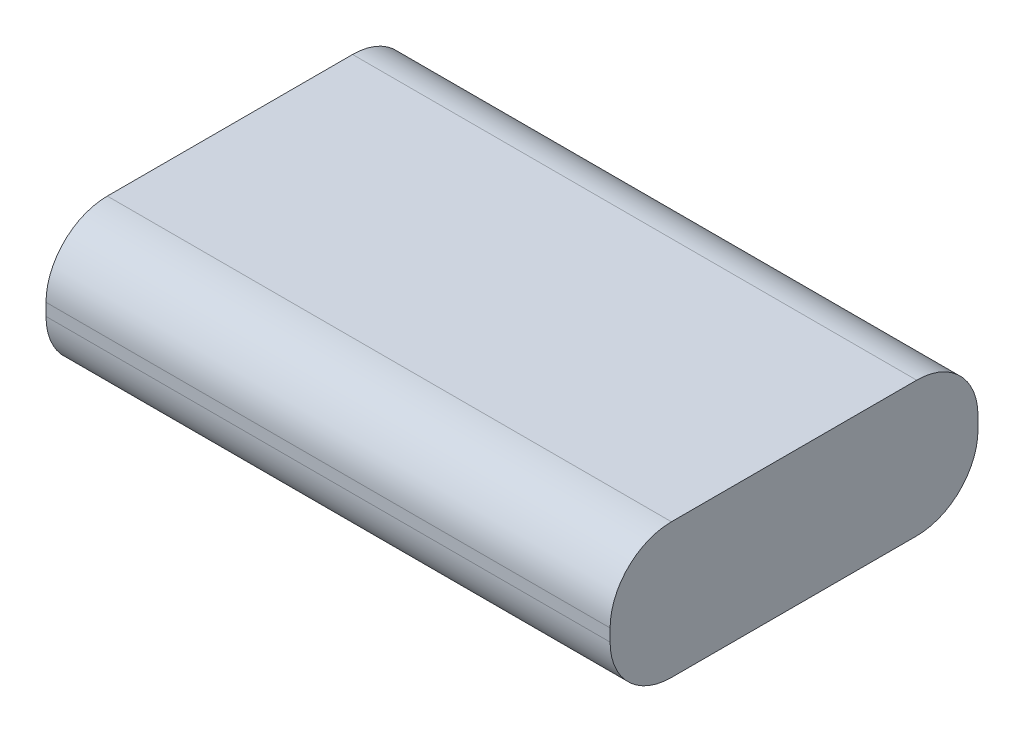
SolidWorks part; units mm, degrees
ref_plane "Front Plane" through (0, 0, 0) normal (0, 0, 1) x (1, 0, 0)
ref_plane "Top Plane" through (0, 0, 0) normal (0, 1, 0) x (1, 0, 0)
ref_plane "Right Plane" through (0, 0, 0) normal (1, 0, 0) x (0, 0, -1)
sketch "Sketch1" plane through (0, 0, 0) normal (0, 1, 0) x (1, 0, 0)
  line L1 (-46, -30) -> (46, -30)
  line L2 (-46, -30) -> (-46, 30)
  line L3 (-46, 30) -> (46, 30)
  line L4 (46, -30) -> (46, 30)
  line L5 (-46, -30) -> (46, 30) construction
  line L6 (-46, 30) -> (46, -30) construction
  point P0 (0, 0)
  dimension "D1" = 92
  dimension "D2" = 60
extrude "Boss-Extrude1" add sketch "Sketch1" along normal blind 22
fillet "Fillet1" radius 10 4 edges at (0, 0, -30) (0, 22, -30) (0, 0, 30) (0, 22, 30)
